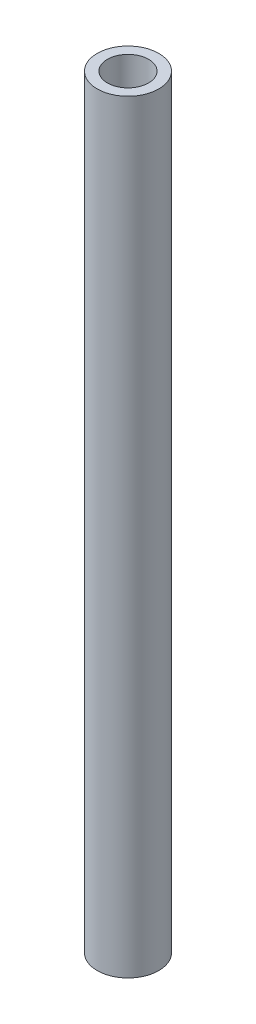
SolidWorks part; units mm, degrees
ref_plane "Front Plane" through (0, 0, 0) normal (0, 0, 1) x (1, 0, 0)
ref_plane "Top Plane" through (0, 0, 0) normal (0, 1, 0) x (1, 0, 0)
ref_plane "Right Plane" through (0, 0, 0) normal (1, 0, 0) x (0, 0, -1)
sketch "Sketch1" plane through (0, 0, 0) normal (0, 1, 0) x (1, 0, 0)
  circle A0 centre (0, 0) radius 25
  circle A1 centre (0, 0) radius 16.7
  dimension "D1" = 50
  dimension "D2" = 8.3
extrude "Boss-Extrude1" add sketch "Sketch1" along normal mid plane 620
